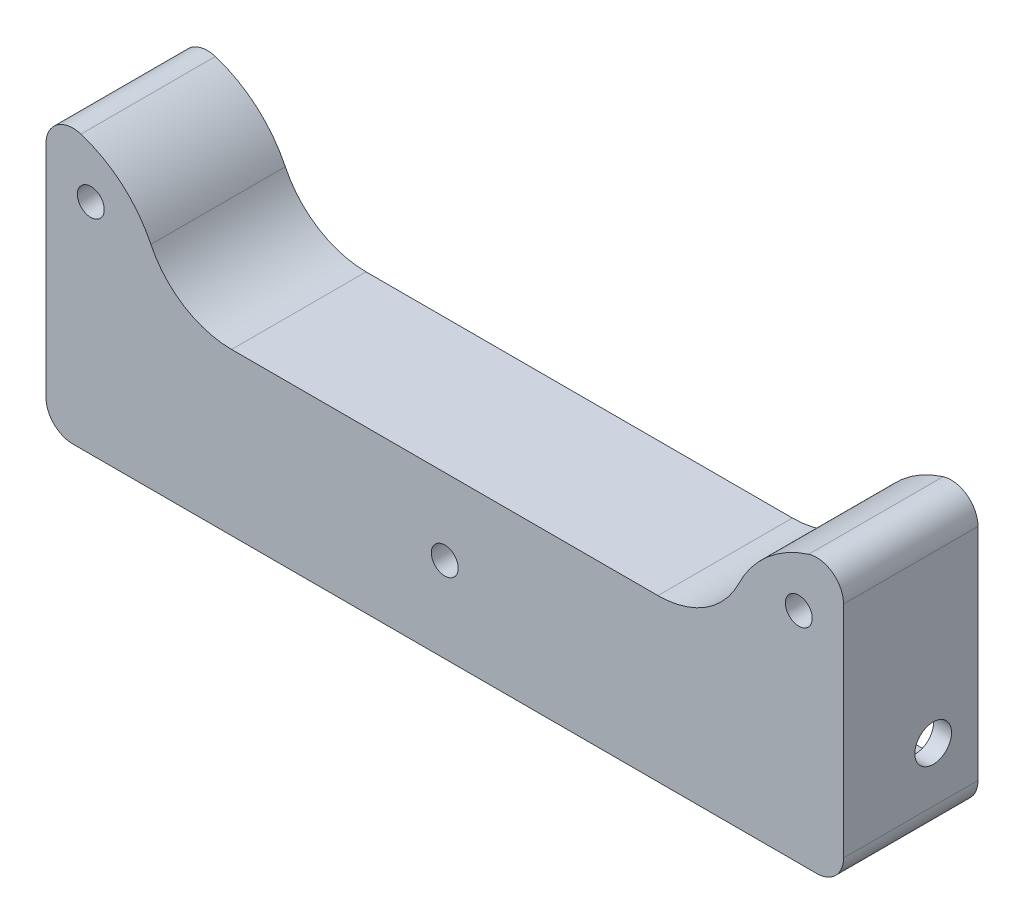
SolidWorks part; units mm, degrees
material "ABS"
ref_plane "Plano frontal" through (0, 0, 0) normal (0, 0, 1) x (1, 0, 0)
ref_plane "Plano superior" through (0, 0, 0) normal (0, 1, 0) x (1, 0, 0)
ref_plane "Plano direito" through (0, 0, 0) normal (1, 0, 0) x (0, 0, -1)
sketch "Esboço1" plane through (0, 0, 0) normal (0, 0, 1) x (1, 0, 0)
  line L0 (33.4361, 75.3989) -> (-49.5639, 75.3989)
  line L11 (10.9361, 93.3989) -> (-27.0639, 93.3989) construction
  line L13 (10.9361, 93.3989) -> (-27.0639, 93.3989)
  line L14 (-52.5639, 78.3989) -> (-52.5639, 93.3989)
  line L15 (-52.5639, 102.9383) -> (-52.5639, 93.3989)
  line L16 (36.4361, 102.9383) -> (36.4361, 93.3989)
  line L18 (15.7238, 93.3989) -> (10.9361, 93.3989)
  line L19 (36.4361, 78.3989) -> (36.4361, 93.3989)
  line L20 (-31.8516, 93.3989) -> (-27.0639, 93.3989)
  arc A0 (-49.5639, 75.3989) -> (-52.5639, 78.3989) centre (-49.5639, 78.3989) cw
  arc A1 (33.4361, 75.3989) -> (36.4361, 78.3989) centre (33.4361, 78.3989) ccw
  arc A6 (36.4361, 102.9383) -> (32.5361, 105.8001) centre (33.4361, 102.9383) ccw
  arc A7 (-40.8569, 99.0511) -> (-48.6639, 105.8001) centre (-52.5639, 93.3989) ccw
  arc A8 (-40.8569, 99.0511) -> (-31.8516, 93.3989) centre (-31.8516, 103.3989) ccw
  arc A9 (-52.5639, 102.9383) -> (-48.6639, 105.8001) centre (-49.5639, 102.9383) cw
  arc A10 (24.7292, 99.0511) -> (15.7238, 93.3989) centre (15.7238, 103.3989) cw
  arc A11 (24.7292, 99.0511) -> (32.5361, 105.8001) centre (36.4361, 93.3989) cw
  point P45 (36.4361, 106.3989)
  point P46 (-52.5639, 106.3989)
  dimension "D1" = 3
extrude "Ressalto-extrusão3" add sketch "Esboço1" along normal blind 15
sketch "Esboço2" plane through (0, 0, 0) normal (0, 0, -1) x (-1, 0, 0)
  line L0 (15.5639, 89.5989) -> (15.5639, 79.3989)
  line L1 (-36.4361, 78.3989) -> (-36.4361, 102.9383) construction
  line L2 (-33.4361, 90.5989) -> (-0.4361, 90.5989)
  line L3 (-34.4361, 89.5989) -> (-34.4361, 79.3989)
  line L4 (-33.4361, 78.3989) -> (-0.4361, 78.3989)
  line L5 (49.5639, 78.3989) -> (16.5639, 78.3989)
  line L6 (50.5639, 89.5989) -> (50.5639, 79.3989)
  line L7 (49.5639, 90.5989) -> (16.5639, 90.5989)
  line L8 (0.5639, 89.5989) -> (0.5639, 79.3989)
  line L9 (49.5639, 75.3989) -> (-33.4361, 75.3989) construction
  line L10 (8.0639, 93.3989) -> (8.0639, 75.3989) construction
  line L11 (-15.7238, 93.3989) -> (31.8516, 93.3989) construction
  line L12 (52.5639, 102.9383) -> (52.5639, 78.3989) construction
  arc A0 (-34.4361, 79.3989) -> (-33.4361, 78.3989) centre (-34.4361, 78.3989) ccw
  arc A1 (-33.4361, 90.5989) -> (-34.4361, 89.5989) centre (-34.4361, 90.5989) ccw
  arc A2 (-0.4361, 78.3989) -> (0.5639, 79.3989) centre (0.5639, 78.3989) ccw
  arc A3 (0.5639, 89.5989) -> (-0.4361, 90.5989) centre (0.5639, 90.5989) ccw
  arc A4 (15.5639, 89.5989) -> (16.5639, 90.5989) centre (15.5639, 90.5989) cw
  arc A5 (16.5639, 78.3989) -> (15.5639, 79.3989) centre (15.5639, 78.3989) cw
  arc A6 (49.5639, 90.5989) -> (50.5639, 89.5989) centre (50.5639, 90.5989) cw
  arc A7 (50.5639, 79.3989) -> (49.5639, 78.3989) centre (50.5639, 78.3989) cw
  dimension "D5" = 2
  dimension "D6" = 2
  dimension "D7" = 2
  dimension "D8" = 2
  dimension "D1" = 2
  dimension "D2" = 3
  dimension "D3" = 12.2
  dimension "D4" = 35
extrude "Corte-extrusão1" cut sketch "Esboço2" against normal blind 10.1
sketch "Esboço3" plane through (0, 0, 0) normal (0, 0, -1) x (-1, 0, 0)
  line L0 (-36.4361, 78.3989) -> (-36.4361, 102.9383) construction
  line L1 (52.5639, 102.9383) -> (52.5639, 78.3989) construction
  line L2 (-15.7238, 93.3989) -> (31.8516, 93.3989) construction
  circle A0 centre (-31.4361, 99.8001) radius 1.5
  circle A1 centre (47.5639, 99.8001) radius 1.5
  circle A2 centre (8.0639, 84.8989) radius 1.5
  point P14 (8.0639, 93.3989)
  dimension "D1" = 5
  dimension "D2" = 3
  dimension "D3" = 6
  dimension "D4" = 5
  dimension "D5" = 6
  dimension "D6" = 3
  dimension "D7" = 8.5
  dimension "D8" = 44.5
  dimension "D9" = 3
extrude "Corte-extrusão2" cut sketch "Esboço3" against normal through all
sketch "Esboço4" plane through (34.4361, 0, 0) normal (-1, 0, 0) x (0, 0, 1)
  line L0 (0, 89.5989) -> (0, 79.3989) construction
  line L1 (0, 79.3989) -> (10, 79.3989) construction
  line L2 (0, 79.3989) -> (0, 89.5989) construction
  line L3 (0, 89.5989) -> (10, 89.5989) construction
  line L4 (10, 79.3989) -> (10, 89.5989) construction
  line L5 (10.1, 89.5989) -> (0, 89.5989) construction
  circle A0 centre (5, 84.4989) radius 2.05
  dimension "D1" = 4.1
  dimension "D2" = 5
  dimension "D3" = 5.1
extrude "Corte-extrusão3" cut sketch "Esboço4" against normal through all
sketch "Esboço5" plane through (-50.5639, 0, 0) normal (1, 0, 0) x (0, 0, -1)
  line L0 (-10.1, 79.3989) -> (0, 79.3989) construction
  line L1 (0, 89.5989) -> (-10, 89.5989) construction
  line L2 (0, 89.5989) -> (0, 79.3989) construction
  line L3 (0, 79.3989) -> (-10, 79.3989) construction
  line L4 (-10, 89.5989) -> (-10, 79.3989) construction
  circle A0 centre (-5, 84.4989) radius 2.05
  dimension "D3" = 5
  dimension "D4" = 5.1
  dimension "D5" = 4.1
  dimension "D6" = 5
  dimension "D1" = 10.2
  dimension "D2" = 10
extrude "Corte-extrusão4" cut sketch "Esboço5" against normal through all
